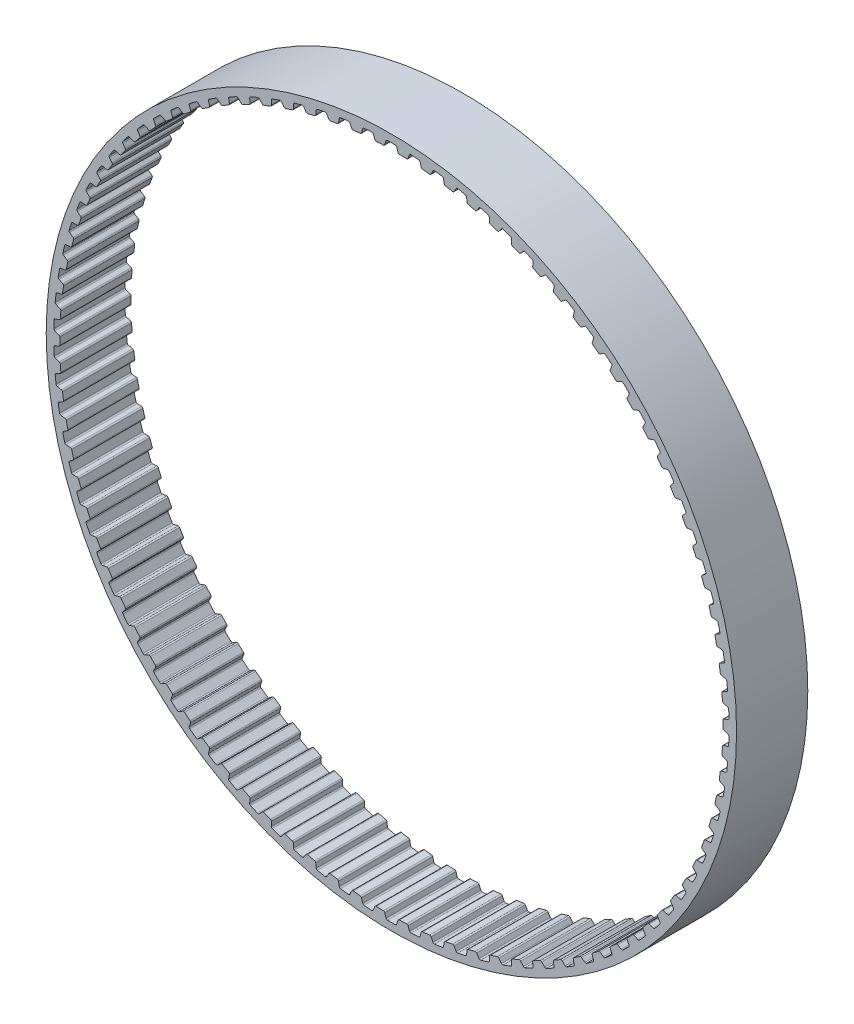
SolidWorks part; units mm, degrees
ref_plane "Front Plane" through (0, 0, 0) normal (0, 0, 1) x (1, 0, 0)
ref_plane "Top Plane" through (0, 0, 0) normal (0, 1, 0) x (1, 0, 0)
ref_plane "Right Plane" through (0, 0, 0) normal (1, 0, 0) x (0, 0, -1)
sketch "Sketch1" plane through (0, 0, 0) normal (0, 0, 1) x (1, 0, 0)
  line L0 (0, 0) -> (-0.9749, 27.9176) construction
  line L1 (0, 0) -> (0.9749, 27.9176) construction
  line L2 (0.9749, 27.9176) -> (-0.9749, 27.9176) construction
  line L3 (0.9749, 27.9176) -> (-0.9749, 27.9176) construction
  circle A0 centre (0, 0) radius 29.0776
  circle A1 centre (0, 0) radius 27.9346
  circle A2 centre (0, 0) radius 28.4426 construction
  dimension "OD" = 58.1553
  dimension "Angle Distance" = 4
  dimension "hs" = 1.143
  dimension "ht" = 0.508
sketch "Sketch4" plane through (0, 0, 0) normal (0, 0, 1) x (1, 0, 0)
  circle A0 centre (0, 0) radius 27.9346 construction
  circle A1 centre (0, 0) radius 29.0776 construction
  circle A2 centre (0, 0) radius 27.9346
  circle A3 centre (0, 0) radius 29.0776
extrude "Boss-Extrude1" add sketch "Sketch4" along normal mid plane 6
sketch "Sketch2" plane through (0, 0, 0) normal (0, 0, 1) x (1, 0, 0)
  line L1 (0, 29.0776) -> (0, 0) construction
  line L2 (-1.015, 28.1854) -> (1.015, 28.1854) construction
  line L4 (-0.5861, 27.9312) -> (-1.3637, 27.904)
  line L5 (-0.5861, 27.9312) -> (-0.4209, 28.4395)
  line L6 (-1.3637, 27.904) -> (-1.5639, 28.3996)
  line L7 (0, 0) -> (-0.9749, 27.9176) construction
  line L8 (-0.4209, 28.4395) -> (-1.5639, 28.3996) construction
  line L9 (0.4209, 28.4395) -> (1.5639, 28.3996) construction
  line L10 (1.3637, 27.904) -> (1.5639, 28.3996)
  line L11 (0.5861, 27.9312) -> (0.4209, 28.4395)
  line L12 (0.5861, 27.9312) -> (1.3637, 27.904)
  line L13 (0, 0) -> (11.1275, 26.8642) construction
  line L14 (-1.015, 28.1854) -> (-3.0397, 28.0393) construction
  line L15 (-2.0274, 28.1123) -> (0, 0) construction
  line L16 (-3.0397, 28.0393) -> (-3.0108, 27.7719) construction
  circle A0 centre (0, 0) radius 28.4426 construction
  circle A1 centre (0, 0) radius 28.4426
  circle A2 centre (0, 0) radius 28.1854 construction
  circle A4 centre (0, 0) radius 29.0776 construction
  circle A5 centre (0, 0) radius 27.9346 construction
  point P16 (-0.5035, 28.1854)
  point P20 (0, 28.1854)
  dimension "D1" = 22.5
  dimension "bt" = 1.143
  dimension "b" = 40
  dimension "Pitch" = 2.03
sketch "Sketch3" plane through (0, 0, 0) normal (0, 0, 1) x (1, 0, 0)
  line L0 (-0.6769, 27.9264) -> (0.6769, 27.9264)
  line L2 (-0.5861, 27.9312) -> (-0.4209, 28.4395) construction
  line L3 (0.5861, 27.9312) -> (0.4209, 28.4395) construction
  line L5 (-0.5591, 28.0141) -> (-0.4491, 28.353)
  line L7 (0.5591, 28.0141) -> (0.4491, 28.353)
  arc A0 (0.5591, 28.0141) -> (0.6769, 27.9264) centre (0.6799, 28.0534) ccw
  circle A1 centre (0, 0) radius 28.4426 construction
  arc A2 (0.3297, 28.4407) -> (-0.3297, 28.4407) centre (0, 0) ccw
  arc A3 (-0.5591, 28.0141) -> (-0.6769, 27.9264) centre (-0.6799, 28.0534) cw
  arc A4 (0.4491, 28.353) -> (0.3297, 28.4407) centre (0.3283, 28.3137) ccw
  arc A5 (-0.4491, 28.353) -> (-0.3297, 28.4407) centre (-0.3283, 28.3137) cw
  circle A6 centre (0, 0) radius 27.9346 construction
  arc A7 (-0.6769, 27.9264) -> (0.6769, 27.9264) centre (0, 0) ccw construction
  dimension "ra" = 0.127
  dimension "rr" = 0.127
extrude "Cut-Extrude1" cut sketch "Sketch3" against normal mid plane 6
pattern_circular "CirPattern1" count 90 over 360 about axis through (0, 0, 0) along (0, 0, 1) of "Cut-Extrude1"
equation "\"D1@Cut-Extrude1\" = \"Width@Boss-Extrude1\""
